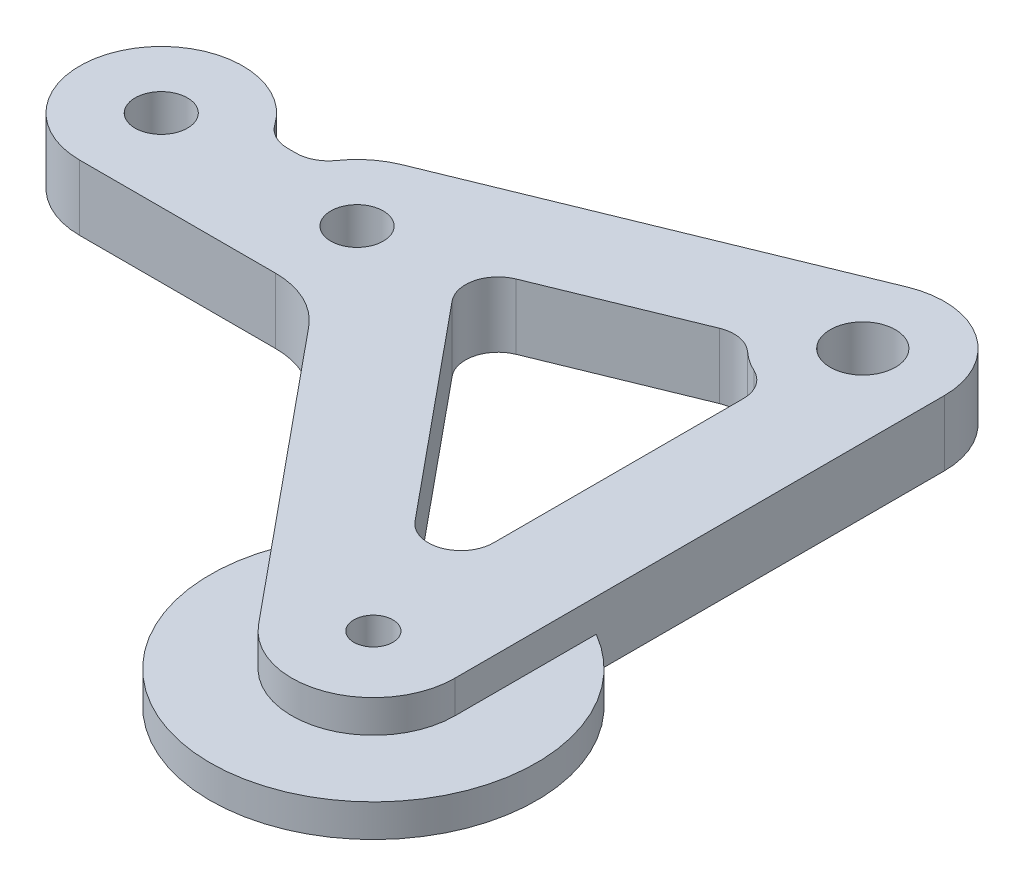
SolidWorks part; units mm, degrees
ref_plane "Front Plane" through (0, 0, 0) normal (0, 0, 1) x (1, 0, 0)
ref_plane "Top Plane" through (0, 0, 0) normal (0, 1, 0) x (1, 0, 0)
ref_plane "Right Plane" through (0, 0, 0) normal (1, 0, 0) x (0, 0, -1)
sketch "Sketch1" plane through (0, 0, 0) normal (0, 1, 0) x (1, 0, 0)
  line L0 (0, -7.9375) -> (19.05, -7.9375)
  line L6 (7.2748, 3.175) -> (11.7752, 3.175)
  line L7 (16.0446, 7.3465) -> (50.9696, 21.634)
  line L8 (61.9125, 14.2875) -> (61.9125, -33.3375)
  line L11 (47.8455, -38.3806) -> (25.1795, -10.8319)
  line L12 (27.2524, 1.6403) -> (52.3875, -28.9094)
  line L13 (52.3875, -28.9094) -> (52.3875, 6.5104)
  line L14 (47.378, 9.8735) -> (27.2524, 1.6403)
  line L21 (-49.2304, 7.7537) -> (-11.7341, 3.0666)
  line L22 (-67.4688, 14.8116) -> (-28.9739, 37.0366)
  line L23 (-18.8945, 35.2284) -> (6.1107, 5.0659)
  line L24 (-50.4241, 13.6538) -> (-30.9466, 24.8991)
  line L25 (-21.2638, 23.1621) -> (-8.896, 8.2435)
  line L26 (-21.6156, 38.5108) -> (-1.0241, 13.6723) construction
  line L27 (-62.7062, 6.5627) -> (-24.2114, 28.7877) construction
  line L28 (-28.9485, 32.4318) -> (-8.357, 7.5932) construction
  line L29 (-64.4845, 0.0613) -> (-0.9845, -7.8762)
  arc A3 (7.2748, 3.175) -> (6.1107, 5.0659) centre (0, 0) ccw
  arc A4 (61.9125, 14.2875) -> (50.9696, 21.634) centre (53.975, 14.2875) ccw
  arc A5 (16.0446, 7.3465) -> (11.7752, 3.175) centre (19.05, 0) ccw
  arc A7 (61.9125, -33.3375) -> (47.8455, -38.3806) centre (53.975, -33.3375) cw
  circle A13 centre (19.05, 0) radius 7.9375 construction
  arc A14 (19.05, -7.9375) -> (25.1795, -10.8319) centre (19.05, -15.875) cw
  arc A15 (-67.4688, 14.8116) -> (-64.4845, 0.0613) centre (-63.5, 7.9375) ccw
  arc A20 (-30.9466, 24.8991) -> (-21.2638, 23.1621) centre (-25.0052, 30.1625) ccw
  arc A21 (-18.8945, 35.2284) -> (-28.9739, 37.0366) centre (-25.0052, 30.1625) ccw
  arc A22 (0, -7.9375) -> (-0.9845, -7.8762) centre (0, 0) cw
  arc A25 (47.378, 9.8735) -> (52.3875, 6.5104) centre (53.975, 14.2875) ccw
  arc A26 (-50.4241, 13.6538) -> (-49.2304, 7.7537) centre (-48.8366, 10.9041) ccw
  arc A27 (-11.7341, 3.0666) -> (-8.896, 8.2435) centre (-11.3403, 6.2171) ccw
  point P24 (20.8393, -5.1327)
  point P25 (52.7163, 5.9798)
  point P26 (45.4914, 11.1125)
  point P27 (45.4914, -42.8625)
  point P28 (50.927, -37.4269)
  point P29 (19.05, -37.4269)
  point P30 (24.4856, -42.8625)
  point P31 (24.4856, -15.875)
  dimension "D4" = 14.2875
  dimension "D1" = 7.9375
  dimension "D6" = 7.9375
  dimension "D7" = 7.9375
  dimension "D10" = 9.525
  dimension "D14" = 6.35
  dimension "D18" = 6.35
  dimension "D2" = 3.175
  dimension "D3" = 19.05
  dimension "D5" = 34.925
  dimension "D8" = 47.625
  dimension "D9" = 9.525
  dimension "D11" = 9.525
  dimension "D12" = 82.55
  dimension "D13" = 9.525
  dimension "D15" = 44.45
  dimension "D16" = 22.225
  dimension "D19" = 7.9375
  dimension "D17" = 9.525
extrude "Boss-Extrude1" add sketch "Sketch1" along normal blind 6.35
fillet "Fillet3" radius 3.175 6 edges at (52.3875, 3.175, 28.9094) (27.2524, 3.175, -1.6403) (-21.2638, 3.175, -23.1621) (-30.9466, 3.175, -24.8991) (52.3875, 3.175, -6.5104) (47.378, 3.175, -9.8735)
hole_wizard "#10 Clearance Hole1" positions "Sketch2" profile "Sketch3" hole size "#10" standard "ANSI Inch" end condition through all
sketch "Sketch2" plane through (0, 6.35, 0) normal (0, 1, 0) x (1, 0, 0)
  point P0 (0, 0)
  point P3 (19.05, 0)
sketch "Sketch3" plane through (0, 6.35, 0) normal (1, 0, 0) x (0, 0, 1)
  line L0 (0, 0) -> (0, 6.35)
  line L1 (0, 6.35) -> (2.5527, 6.35)
  line L2 (2.5527, 6.35) -> (2.5527, 0)
  line L5 (2.5527, 0) -> (0, 0)
  line L11 (0, -6.35) -> (0, 107.95) construction
  dimension "Thru Hole Dia." = 5.1054
  dimension "Thru Hole Depth" = 6.35
hole_wizard "1/4 (0.25) Diameter Hole1" positions "Sketch4" profile "Sketch5" hole size "1/4" standard "ANSI Inch" end condition through all
sketch "Sketch4" plane through (0, 6.35, 0) normal (0, 1, 0) x (1, 0, 0)
  point P0 (53.975, 14.2875)
  point P12 (-63.5, 7.9375)
sketch "Sketch5" plane through (53.975, 6.35, -14.2875) normal (1, 0, 0) x (0, 0, 1)
  line L0 (0, 0) -> (0, 6.35)
  line L1 (0, 6.35) -> (3.175, 6.35)
  line L2 (3.175, 6.35) -> (3.175, 0)
  line L5 (3.175, 0) -> (0, 0)
  line L11 (0, -6.35) -> (0, 107.95) construction
  dimension "Thru Hole Dia." = 6.35
  dimension "Thru Hole Depth" = 6.35
fillet "Fillet2" radius 3.175 2 edges at (11.7752, 3.175, -3.175) (7.2748, 3.175, -3.175)
hole_wizard "#10-24 Tapped Hole1" positions "Sketch6" profile "Sketch7" tap size "#10-24" standard "ANSI Inch" end condition through all
sketch "Sketch6" plane through (0, 6.35, 0) normal (0, 1, 0) x (1, 0, 0)
  point P0 (53.975, -33.3375)
  point P9 (-25.0052, 30.1625)
sketch "Sketch7" plane through (53.975, 6.35, 33.3375) normal (1, 0, 0) x (0, 0, 1)
  line L0 (0, 0) -> (0, 6.35)
  line L1 (0, 6.35) -> (1.8986, 6.35)
  line L2 (1.8986, 6.35) -> (1.8986, 0)
  line L5 (1.8986, 0) -> (0, 0)
  line L11 (0, -6.35) -> (0, 107.95) construction
  dimension "Thru Tap Drill Dia." = 3.7973
  dimension "Thru Tap Drill Depth" = 6.35
cosmetic thread "Hole Thread1" parameters "D2"=4.826
cosmetic thread "Hole Thread4" parameters "D2"=4.826
sketch "Sketch8" plane through (0, 6.35, 0) normal (0, 1, 0) x (1, 0, 0)
  line L0 (61.9125, -33.3375) -> (61.9125, 14.2875) construction
  line L1 (25.1795, -10.8319) -> (47.8455, -38.3806) construction
  line L2 (39.1106, -27.764) -> (47.8455, -38.3806)
  line L3 (61.9125, -33.3375) -> (61.9125, -19.5893)
  line L8 (-28.9739, 37.0366) -> (-67.4688, 14.8116) construction
  line L9 (6.1107, 5.0659) -> (-18.8945, 35.2284) construction
  line L10 (-28.9739, 37.0366) -> (-40.8802, 30.1625)
  line L11 (-10.1201, 24.6443) -> (-18.8945, 35.2284)
  arc A0 (39.1106, -27.764) -> (61.9125, -19.5893) centre (53.975, -33.3375) ccw
  arc A1 (47.8455, -38.3806) -> (61.9125, -33.3375) centre (53.975, -33.3375) ccw construction
  arc A2 (47.8455, -38.3806) -> (61.9125, -33.3375) centre (53.975, -33.3375) ccw
  arc A3 (-10.1201, 24.6443) -> (-40.8802, 30.1625) centre (-25.0052, 30.1625) ccw
  arc A6 (-18.8945, 35.2284) -> (-28.9739, 37.0366) centre (-25.0052, 30.1625) ccw construction
  arc A7 (-18.8945, 35.2284) -> (-28.9739, 37.0366) centre (-25.0052, 30.1625) ccw
  dimension "D1" = 31.75
extrude "Boss-Extrude2" add sketch "Sketch8" against normal up to surface (3.175 mm away) from offset 3.175 contours A0 L3 A2 L2 | L10 A3 L11 A7 up to face at (53.975, 0, 35.2361) offset against normal yes
sketch "Sketch9" plane through (0, 6.35, 0) normal (0, 1, 0) x (1, 0, 0)
  line L2 (-18.8945, 35.2284) -> (-10.1201, 24.6443)
  line L3 (-40.8802, 30.1625) -> (-28.9739, 37.0366)
  line L8 (0, -7.9375) -> (19.05, -7.9375)
  line L9 (25.1795, -10.8319) -> (47.8455, -38.3806)
  line L10 (61.9125, -33.3375) -> (61.9125, 14.2875)
  line L11 (50.9696, 21.634) -> (16.0446, 7.3465)
  line L12 (9.9305, 3.175) -> (9.1195, 3.175)
  line L13 (6.1107, 5.0659) -> (-18.8945, 35.2284)
  line L14 (-28.9739, 37.0366) -> (-67.4688, 14.8116)
  line L15 (-64.4845, 0.0613) -> (-0.9845, -7.8762)
  line L21 (6.1107, 5.0659) -> (-10.1201, 24.6443)
  line L22 (-40.8802, 30.1625) -> (-67.4688, 14.8116)
  line L23 (-64.4845, 0.0613) -> (-0.9845, -7.8762)
  arc A0 (6.1107, 5.0659) -> (-0.9845, -7.8762) centre (0, 0) ccw
  arc A3 (-18.8945, 35.2284) -> (-28.9739, 37.0366) centre (-25.0052, 30.1625) ccw
  arc A4 (-10.1201, 24.6443) -> (-40.8802, 30.1625) centre (-25.0052, 30.1625) ccw
  arc A6 (-10.1201, 24.6443) -> (-40.8802, 30.1625) centre (-25.0052, 30.1625) ccw
  arc A10 (-0.9845, -7.8762) -> (0, -7.9375) centre (0, 0) ccw
  arc A11 (25.1795, -10.8319) -> (19.05, -7.9375) centre (19.05, -15.875) ccw
  arc A12 (47.8455, -38.3806) -> (61.9125, -33.3375) centre (53.975, -33.3375) ccw
  arc A13 (61.9125, 14.2875) -> (50.9696, 21.634) centre (53.975, 14.2875) ccw
  arc A14 (16.0446, 7.3465) -> (12.5361, 4.5357) centre (19.05, 0) ccw
  arc A15 (9.9305, 3.175) -> (12.5361, 4.5357) centre (9.9305, 6.35) ccw
  arc A16 (6.5139, 4.5357) -> (9.1195, 3.175) centre (9.1195, 6.35) ccw
  arc A17 (6.5139, 4.5357) -> (6.1107, 5.0659) centre (0, 0) ccw
  arc A18 (-18.8945, 35.2284) -> (-28.9739, 37.0366) centre (-25.0052, 30.1625) ccw
  arc A19 (-67.4688, 14.8116) -> (-64.4845, 0.0613) centre (-63.5, 7.9375) ccw
  arc A29 (-67.4688, 14.8116) -> (-64.4845, 0.0613) centre (-63.5, 7.9375) ccw
  dimension "D1" = 0
  dimension "D2" = 0
extrude "Cut-Extrude1" cut sketch "Sketch9" against normal through all
